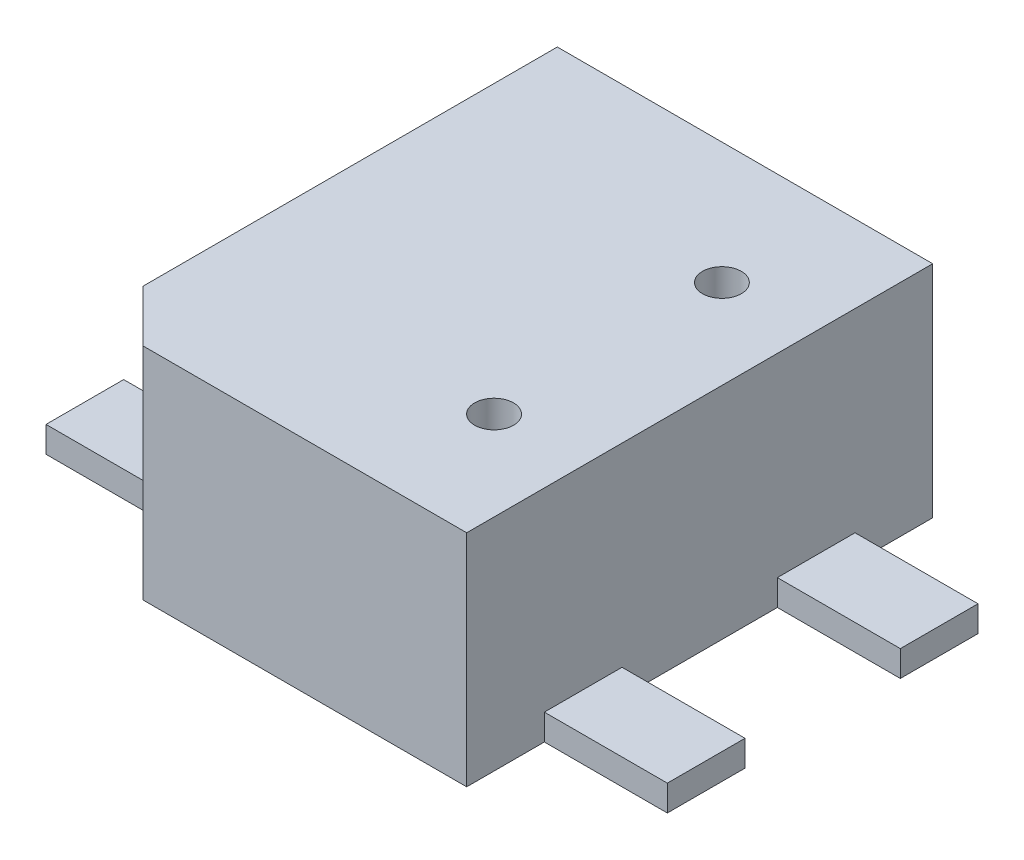
SolidWorks part; units mm, degrees
ref_plane "Front Plane" through (0, 0, 0) normal (0, 0, 1) x (1, 0, 0)
ref_plane "Top Plane" through (0, 0, 0) normal (0, 1, 0) x (1, 0, 0)
ref_plane "Right Plane" through (0, 0, 0) normal (1, 0, 0) x (0, 0, -1)
sketch "스케치1" plane through (0, 0, 0) normal (0, 1, 0) x (1, 0, 0)
  line L1 (-1.45, 1.8) -> (1.45, 1.8)
  line L2 (-1.45, 1.8) -> (-1.45, -1.8)
  line L3 (-1.45, -1.8) -> (1.45, -1.8)
  line L4 (1.45, 1.8) -> (1.45, -1.8)
  dimension "D1" = 2.9
  dimension "D2" = 3.6
  dimension "D3" = 1.45
  dimension "D4" = 1.8
extrude "보스-돌출1" add sketch "스케치1" along normal blind 1.7
sketch "스케치3" plane through (0, 1.7, 0) normal (0, 1, 0) x (1, 0, 0)
  line L0 (-2.4401, -1.4) -> (49997.5599, -1.4) construction
  line L1 (-1.05, -1.9186) -> (-1.05, 49998.0814) construction
  line L2 (-1.45, 1.8) -> (-1.45, -1.8) construction
  line L3 (-1.45, -1.8) -> (1.45, -1.8) construction
  line L4 (-1.4505, -1.4) -> (-1.05, -1.8005)
  line L5 (-1.05, -1.8005) -> (-1.45, -1.8)
  line L6 (-1.45, -1.8) -> (-1.4505, -1.4)
  dimension "D1" = 0.4
  dimension "D2" = 0.4
extrude "컷-돌출1" cut sketch "스케치3" against normal blind 1.7
sketch "스케치5" plane through (0, 0, 0) normal (0, -1, 0) x (1, 0, 0)
  line L0 (-2.4, -0.3905) -> (-2.4, 49999.6095) construction
  line L1 (2.4, -0.342) -> (2.4, 49999.658) construction
  line L2 (-1.8046, -1.2) -> (49998.1954, -1.2) construction
  line L3 (-2.9592, -0.6) -> (49997.0408, -0.6) construction
  line L4 (-2.9155, 0.6) -> (49997.0845, 0.6) construction
  line L5 (-2.7312, 1.2) -> (49997.2688, 1.2) construction
  line L6 (0, 0) -> (0, 50000) construction
  line L7 (0, 0) -> (50000, 0) construction
  line L9 (-2.4, -1.2) -> (2.4, -1.2)
  line L10 (-2.4, -1.2) -> (-2.4, -0.6)
  line L11 (-2.4, -0.6) -> (2.4, -0.6)
  line L12 (2.4, -1.2) -> (2.4, -0.6)
  line L13 (-2.4, 0.6) -> (2.4, 0.6)
  line L14 (-2.4, 0.6) -> (-2.4, 1.2)
  line L15 (-2.4, 1.2) -> (2.4, 1.2)
  line L16 (2.4, 0.6) -> (2.4, 1.2)
  dimension "D1" = 2.4
  dimension "D2" = 2.4
  dimension "D3" = 1.2
  dimension "D4" = 1.2
  dimension "D5" = 0.6
  dimension "D6" = 0.6
extrude "보스-돌출2" add sketch "스케치5" against normal blind 0.2
sketch "스케치4" plane through (0, 1.7, 0) normal (0, 1, 0) x (1, 0, 0)
  line L0 (0.7616, 0.6719) -> (0.7616, -49999.3281) construction
  line L1 (-1.8822, 0.86) -> (2.2121, 0.86) construction
  line L2 (-1.8095, -0.86) -> (2.1781, -0.86) construction
  line L3 (0, 0) -> (50000, 0) construction
  line L4 (1.45, -1.8) -> (1.45, 1.8) construction
  line L5 (1.45, 1.8) -> (-1.45, 1.8) construction
  line L6 (-1.0505, -1.8) -> (1.45, -1.8) construction
  circle A0 centre (0.7616, 0.86) radius 0.15
  circle A1 centre (0.7616, -0.9) radius 0.15
  dimension "D1" = 0.6884
  dimension "D2" = 0.94
  dimension "D3" = 0.94
extrude "컷-돌출2" cut sketch "스케치4" against normal blind 1.7
sketch "스케치6" plane through (0, 1.7, 0) normal (0, 1, 0) x (1, 0, 0)
  line L0 (0, 0) -> (0, 50000) construction
  line L1 (0.7616, 0.86) -> (0.7616, -49999.14) construction
